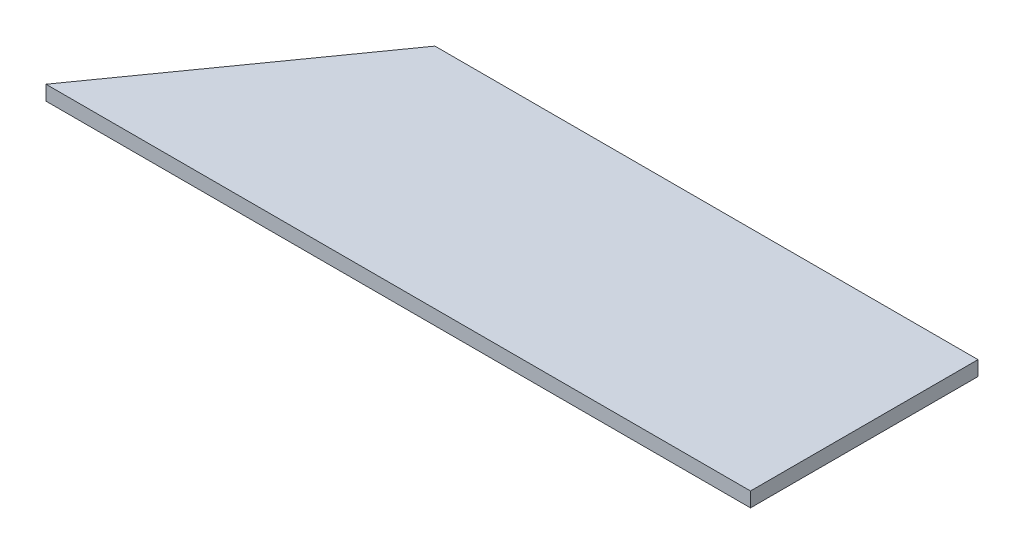
SolidWorks part; units mm, degrees
ref_plane "Front Plane" through (0, 0, 0) normal (0, 0, 1) x (1, 0, 0)
ref_plane "Top Plane" through (0, 0, 0) normal (0, 1, 0) x (1, 0, 0)
ref_plane "Right Plane" through (0, 0, 0) normal (1, 0, 0) x (0, 0, -1)
sketch "Sketch1" plane through (0, 0, 0) normal (0, 1, 0) x (1, 0, 0)
  line L0 (0, 0) -> (304.8, 0)
  line L1 (304.8, 0) -> (304.8, 98.425)
  line L2 (304.8, 98.425) -> (69.85, 98.425)
  line L3 (69.85, 98.425) -> (0, 0)
  dimension "D1" = 98.425
  dimension "D2" = 304.8
  dimension "D3" = 234.95
extrude "Boss-Extrude1" add sketch "Sketch1" along normal blind 6.35
